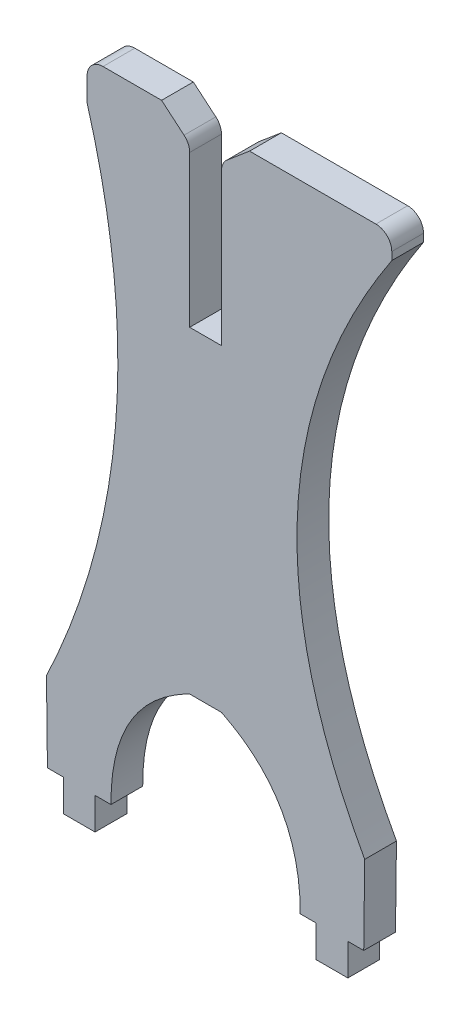
SolidWorks part; units mm, degrees
ref_plane "Front Plane" through (0, 0, 0) normal (0, 0, 1) x (1, 0, 0)
ref_plane "Top Plane" through (0, 0, 0) normal (0, 1, 0) x (1, 0, 0)
ref_plane "Right Plane" through (0, 0, 0) normal (1, 0, 0) x (0, 0, -1)
sketch "Sketch1" plane through (0, 0, 0) normal (0, 0, 1) x (1, 0, 0)
  line L17 (0.1483, -16.543) -> (-0.0059, -3.8439)
  line L47 (6.5002, 85.057) -> (6.5002, 78.707)
  line L57 (6.5002, 85.057) -> (18.4064, 85.057)
  line L67 (0.1483, -16.543) -> (2.6883, -16.543)
  line L71 (7.7683, -16.543) -> (10.3083, -16.543)
  line L74 (2.6883, -16.543) -> (2.6883, -21.623)
  line L75 (2.6883, -21.623) -> (7.7683, -21.623)
  line L76 (7.7683, -16.543) -> (7.7683, -21.623)
  line L102 (22.9031, 55.863) -> (22.9031, 81.263)
  line L105 (22.9031, 81.263) -> (18.4064, 85.057)
  line L108 (27.9831, 55.863) -> (27.9831, 81.263)
  line L109 (27.9831, 81.263) -> (32.4797, 85.057)
  line L110 (27.9831, 55.863) -> (22.9031, 55.863)
  line L112 (27.9831, 5.063) -> (22.9031, 5.063)
  line L113 (55.2236, 85.057) -> (32.4797, 85.057)
  line L114 (55.2236, 85.057) -> (55.2236, 81.263)
  line L115 (50.7378, -16.543) -> (50.892, -3.8439)
  line L116 (50.7378, -16.543) -> (48.1978, -16.543)
  line L117 (48.1978, -16.543) -> (48.1978, -21.623)
  line L118 (48.1978, -21.623) -> (43.1178, -21.623)
  line L119 (43.1178, -16.543) -> (43.1178, -21.623)
  line L120 (43.1178, -16.543) -> (40.5778, -16.543)
  spline S0 degree 2 poles (6.5002, 78.707) (18.9018, 35.9899) (-0.0059, -3.8439) knots 0 0 0 1 1 1
  spline S1 degree 2 poles (22.9031, 5.063) (10.2023, -1.2212) (10.3083, -16.543) knots 0 0 0 1 1 1
  spline S2 degree 2 poles (55.2236, 81.263) (27.243, 39.094) (50.892, -3.8439) knots 0 0 0 1 1 1
  spline S3 degree 2 poles (27.9831, 5.063) (40.6838, -1.2212) (40.5778, -16.543) knots 0 0 0 1 1 1
  point P5 (0, 0)
  point P11 (0, 0)
  point P31 (0, 0)
  point P32 (0, 0)
  point P34 (50.7313, 81.263)
  point P35 (0, 0)
  dimension "D8" = 11.9062
  dimension "D2" = 6.35
  dimension "D3" = 50.8
  dimension "D4" = 10.16
  dimension "D7" = 12.7
  dimension "D10" = 5.08
  dimension "D11" = 5.08
extrude "Boss-Extrude6" add sketch "Sketch1" along normal blind 5.08 separate body
fillet "Fillet21" radius 2.54 1 edges at (22.9031, 81.263, 2.54)
fillet "Fillet22" radius 2.54 1 edges at (27.9831, 81.263, 2.54)
fillet "Fillet23" radius 2.54 1 edges at (6.5002, 85.057, 2.54)
fillet "Fillet24" radius 2.54 1 edges at (55.2236, 85.057, 2.54)
